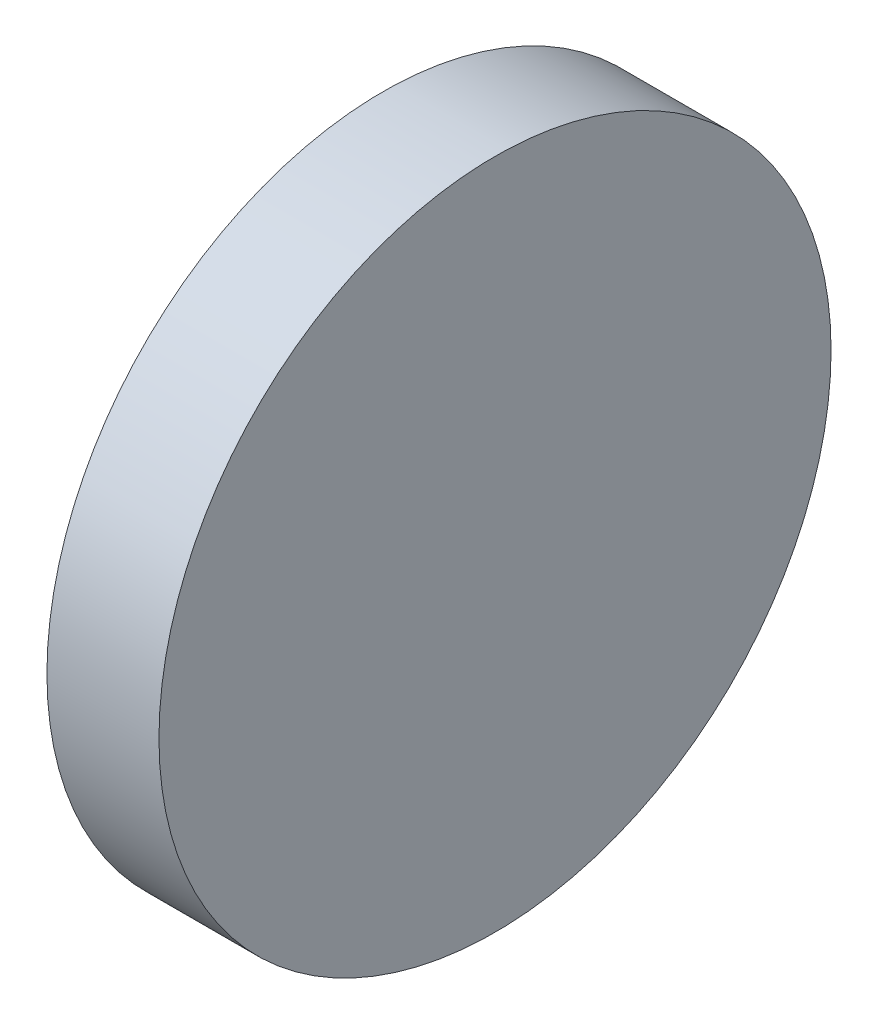
SolidWorks part; units mm, degrees
ref_plane "前视基准面" through (0, 0, 0) normal (0, 0, 1) x (1, 0, 0)
ref_plane "上视基准面" through (0, 0, 0) normal (0, 1, 0) x (1, 0, 0)
ref_plane "右视基准面" through (0, 0, 0) normal (1, 0, 0) x (0, 0, -1)
sketch "草图1" plane through (0, 0, 0) normal (0, 0, 1) x (1, 0, 0)
  line L0 (0, 3) -> (0, 0)
  line L2 (0, 3) -> (1, 3)
  line L3 (0, 0) -> (1, 0)
  line L4 (1, 3) -> (1, 0)
  dimension "D1" = 3
  dimension "D2" = 1
revolve "旋转2" add sketch "草图1" angle 360 about L3
